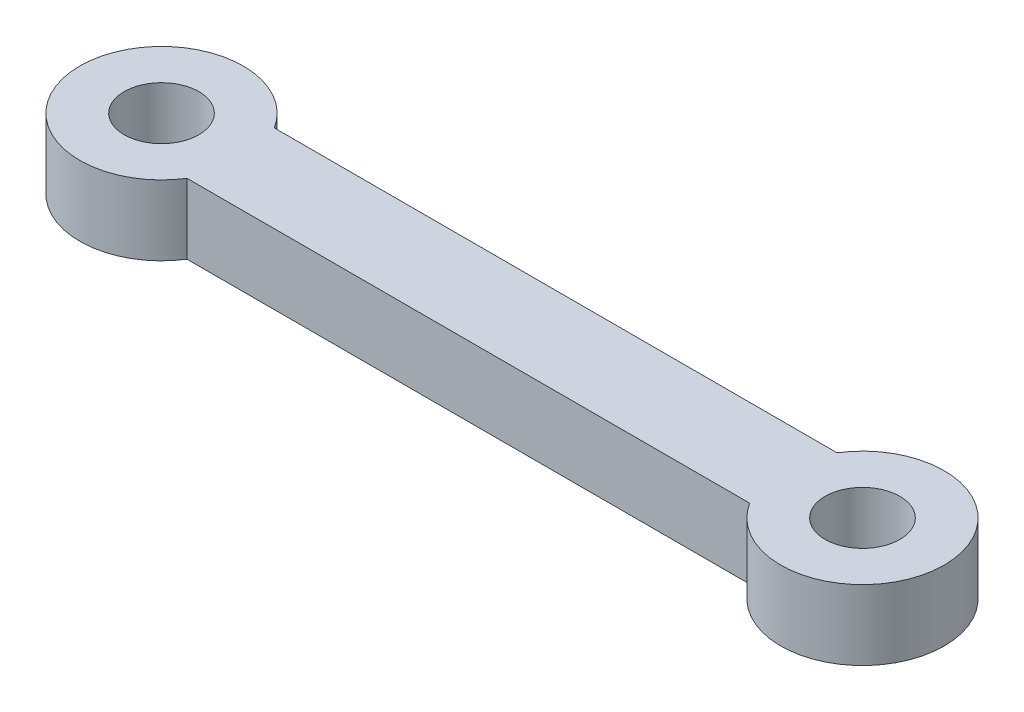
SolidWorks part; units mm, degrees
ref_plane "Front Plane" through (0, 0, 0) normal (0, 0, 1) x (1, 0, 0)
ref_plane "Top Plane" through (0, 0, 0) normal (0, 1, 0) x (1, 0, 0)
ref_plane "Right Plane" through (0, 0, 0) normal (1, 0, 0) x (0, 0, -1)
sketch "Sketch1" plane through (0, 0, 0) normal (0, 1, 0) x (1, 0, 0)
  line L0 (0, 0) -> (30, 0) construction
  line L1 (0, 3.5) -> (30, 3.5) construction
  line L2 (0, -3.5) -> (30, -3.5) construction
  line L4 (2.9598, -1.8681) -> (27.0402, -1.8681)
  line L5 (2.9598, -1.8681) -> (2.9598, 1.8681) construction
  line L6 (2.9598, 1.8681) -> (27.0402, 1.8681)
  line L7 (27.0402, -1.8681) -> (27.0402, 1.8681) construction
  line L8 (2.9598, -1.8681) -> (27.0402, 1.8681) construction
  line L9 (2.9598, 1.8681) -> (27.0402, -1.8681) construction
  arc A0 (0, 3.5) -> (0, -3.5) centre (0, 0) ccw construction
  arc A1 (30, -3.5) -> (30, 3.5) centre (30, 0) ccw construction
  circle A2 centre (30, 0) radius 3.5
  circle A3 centre (0, 0) radius 3.5
  circle A4 centre (0, 0) radius 1.6
  circle A5 centre (30, 0) radius 1.6
  point P3 (15, 0)
  point P12 (15, 0)
  dimension "D3" = 3.2
  dimension "D4" = 3.2
  dimension "D5" = 3.2
  dimension "D1" = 30
  dimension "D2" = 7
extrude "Boss-Extrude1" add sketch "Sketch1" along normal blind 3 contours A3 A4 | A2 A5 | A3 L4 A2 L6
